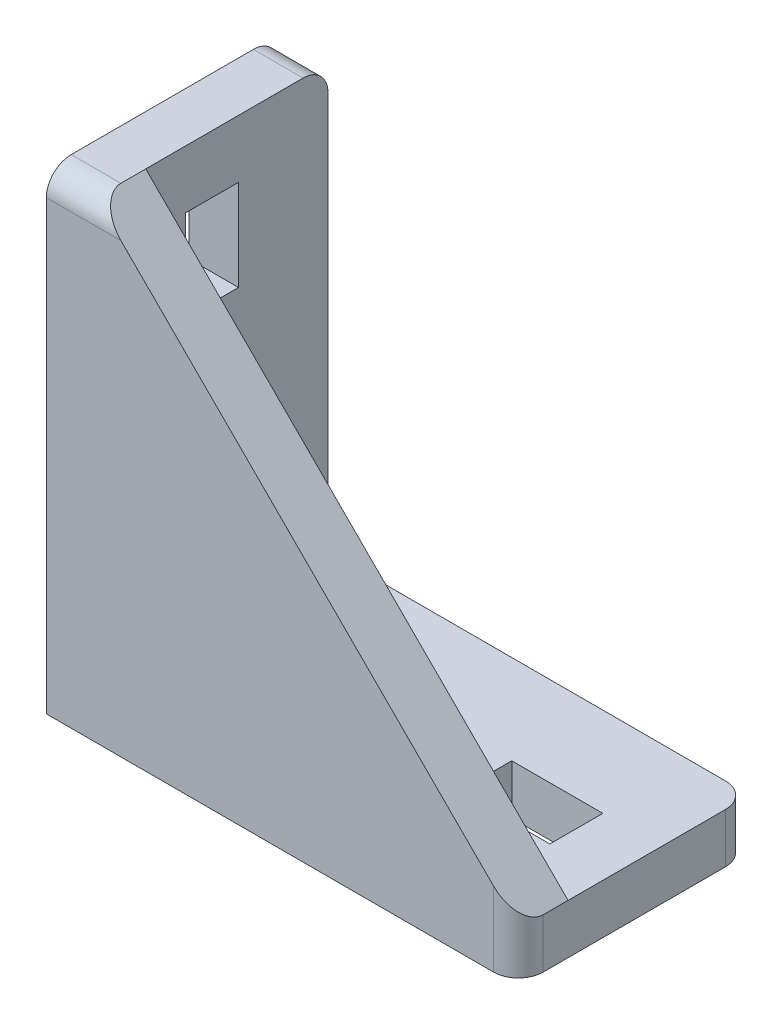
SolidWorks part; units mm, degrees
ref_plane "Ebene vorne" through (0, 0, 0) normal (0, 0, 1) x (1, 0, 0)
ref_plane "Ebene oben" through (0, 0, 0) normal (0, 1, 0) x (1, 0, 0)
ref_plane "Ebene rechts" through (0, 0, 0) normal (1, 0, 0) x (0, 0, -1)
sketch "Skizze1" plane through (0, 0, 0) normal (0, 0, 1) x (1, 0, 0)
  line L0 (0, 0) -> (0, 57)
  line L1 (0, 57) -> (6, 57)
  line L2 (6, 57) -> (6, 6)
  line L3 (6, 6) -> (57, 6)
  line L4 (57, 6) -> (57, 0)
  line L5 (57, 0) -> (0, 0)
  dimension "D1" = 57
  dimension "D2" = 57
  dimension "D3" = 6
  dimension "D4" = 6
extrude "Aufsatz-Linear austragen1" add sketch "Skizze1" along normal blind 28
sketch "Skizze2" plane through (0, 0, 28) normal (0, 0, 1) x (1, 0, 0)
  line L0 (6, 57) -> (6, 6)
  line L1 (6, 6) -> (57, 6)
  line L2 (57, 6) -> (6, 57)
extrude "Aufsatz-Linear austragen2" add sketch "Skizze2" against normal blind 6
sketch "Skizze3" plane through (6, 0, 0) normal (1, 0, 0) x (0, 0, -1)
  line L0 (-14, 57) -> (-14, 6) construction
  line L1 (-22, 57) -> (0, 57) construction
  line L2 (-22, 6) -> (0, 6) construction
  line L3 (-28, 6) -> (-28, 57) construction
  line L4 (-28, 0) -> (0, 0) construction
  line L5 (-17.2, 39) -> (-10.8, 39)
  line L6 (-17.2, 39) -> (-17.2, 50)
  line L7 (-17.2, 50) -> (-10.8, 50)
  line L8 (-10.8, 39) -> (-10.8, 50)
  line L9 (-17.2, 39) -> (-10.8, 50) construction
  line L10 (-17.2, 50) -> (-10.8, 39) construction
  line L11 (-17.2, 10) -> (-10.8, 10)
  line L12 (-17.2, 10) -> (-17.2, 20)
  line L13 (-17.2, 20) -> (-10.8, 20)
  line L14 (-10.8, 10) -> (-10.8, 20)
  line L15 (-17.2, 10) -> (-10.8, 20) construction
  line L16 (-17.2, 20) -> (-10.8, 10) construction
  point P8 (-14, 44.5)
  point P13 (-14, 15)
  dimension "D1" = 14
  dimension "D2" = 6.4
  dimension "D3" = 6.4
  dimension "D4" = 11
  dimension "D5" = 10
  dimension "D6" = 50
  dimension "D7" = 20
extrude "Schnitt-Linear austragen1" cut sketch "Skizze3" against normal through all
sketch "Skizze4" plane through (0, 6, 0) normal (0, 1, 0) x (1, 0, 0)
  line L0 (57, -14) -> (6, -14) construction
  line L1 (57, -22) -> (57, 0) construction
  line L2 (6, -22) -> (6, 0) construction
  line L3 (57, -28) -> (6, -28) construction
  line L4 (0, -28) -> (0, 0) construction
  line L5 (39, -10.8) -> (50, -10.8)
  line L6 (39, -10.8) -> (39, -17.2)
  line L7 (39, -17.2) -> (50, -17.2)
  line L8 (50, -10.8) -> (50, -17.2)
  line L9 (39, -10.8) -> (50, -17.2) construction
  line L10 (39, -17.2) -> (50, -10.8) construction
  line L11 (10, -10.8) -> (20, -10.8)
  line L12 (10, -10.8) -> (10, -17.2)
  line L13 (10, -17.2) -> (20, -17.2)
  line L14 (20, -10.8) -> (20, -17.2)
  line L15 (10, -10.8) -> (20, -17.2) construction
  line L16 (10, -17.2) -> (20, -10.8) construction
  point P8 (44.5, -14)
  point P13 (15, -14)
  point P18 (50, -14)
  dimension "D1" = 14
  dimension "D2" = 10
  dimension "D3" = 11
  dimension "D4" = 6.4
  dimension "D5" = 6.4
  dimension "D6" = 50
  dimension "D7" = 20
extrude "Schnitt-Linear austragen2" cut sketch "Skizze4" against normal through all
fillet "Verrundung1" radius 3 4 edges at (57, 3, 28) (3, 57, 28) (3, 57, 0) (57, 3, 0)
